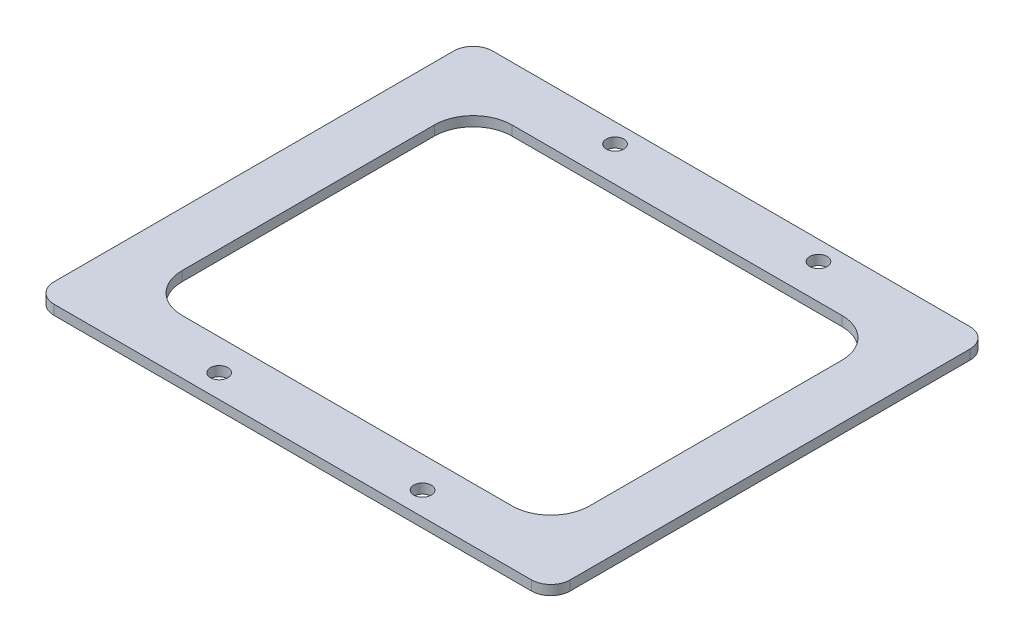
SolidWorks part; units mm, degrees
ref_plane "Front Plane" through (0, 0, 0) normal (0, 0, 1) x (1, 0, 0)
ref_plane "Top Plane" through (0, 0, 0) normal (0, 1, 0) x (1, 0, 0)
ref_plane "Right Plane" through (0, 0, 0) normal (1, 0, 0) x (0, 0, -1)
sketch "Sketch1" plane through (0, 0, 0) normal (0, 1, 0) x (1, 0, 0)
  line L0 (-84.455, -71.755) -> (-84.455, 71.755)
  line L1 (66.675, -53.975) -> (-66.675, -53.975)
  line L2 (66.675, -53.975) -> (66.675, 53.975)
  line L3 (66.675, 53.975) -> (-66.675, 53.975)
  line L4 (-66.675, -53.975) -> (-66.675, 53.975)
  line L5 (66.675, -53.975) -> (-66.675, 53.975) construction
  line L6 (66.675, 53.975) -> (-66.675, -53.975) construction
  line L7 (84.455, 71.755) -> (-84.455, 71.755)
  line L8 (84.455, -71.755) -> (84.455, 71.755)
  line L9 (84.455, -71.755) -> (-84.455, -71.755)
  point P0 (0, 0)
  dimension "D1" = 107.95
  dimension "D2" = 133.35
  dimension "D3" = 17.78
extrude "Boss-Extrude1" add sketch "Sketch1" along normal blind 3.175
fillet "Fillet1" radius 6.35 4 edges at (-84.455, 1.5875, -71.755) (84.455, 1.5875, -71.755) (84.455, 1.5875, 71.755) (-84.455, 1.5875, 71.755)
fillet "Fillet2" radius 12.7 4 edges at (66.675, 1.5875, 53.975) (-66.675, 1.5875, 53.975) (-66.675, 1.5875, -53.975) (66.675, 1.5875, -53.975)
sketch "Sketch2" plane through (0, 3.175, 0) normal (0, 1, 0) x (1, 0, 0)
  line L1 (-84.455, -71.755) -> (-84.455, 71.755) construction
  line L2 (66.675, 53.975) -> (-66.675, 53.975) construction
  circle A0 centre (-31.6865, 65.405) radius 2.8575
  dimension "D1" = 5.715
  dimension "D2" = 11.43
  dimension "D3" = 52.7685
extrude "Cut-Extrude1" cut sketch "Sketch2" against normal through all
pattern_linear "LPattern1" count 2 spacing 66.548 along (1, 0, 0) count 2 spacing 129.54 along (0, 0, 1) of "Cut-Extrude1"
